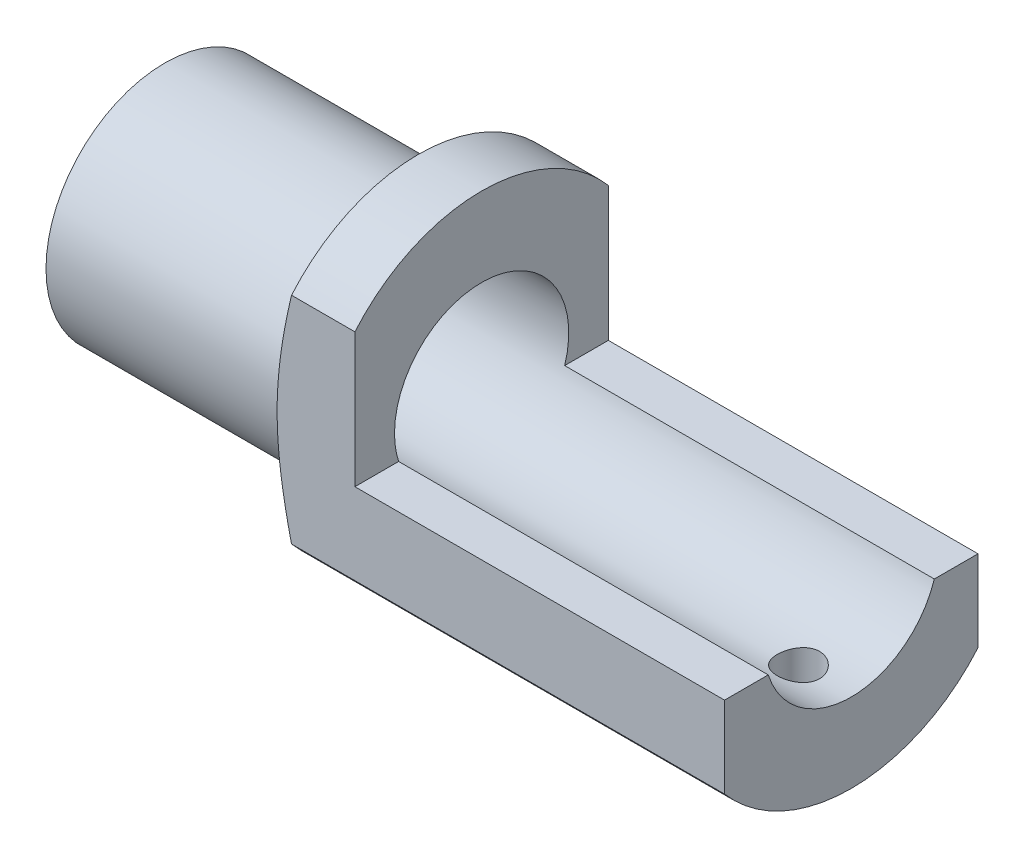
SolidWorks part; units mm, degrees
material "ПТФЭ (общий)"
ref_plane "Спереди" through (0, 0, 0) normal (0, 0, 1) x (1, 0, 0)
ref_plane "Сверху" through (0, 0, 0) normal (0, 1, 0) x (1, 0, 0)
ref_plane "Справа" through (0, 0, 0) normal (1, 0, 0) x (0, 0, -1)
sketch "Эскиз1" plane through (0, 0, 0) normal (0, 0, 1) x (1, 0, 0)
  line L0 (0, 0) -> (12.5645, 0) construction
  line L1 (0, 1.65) -> (13, 1.65)
  line L2 (13, 1.65) -> (13, 3.15)
  line L3 (13, 3.15) -> (4.5, 3.15)
  line L4 (4.5, 3.15) -> (4.5, 2.25)
  line L5 (4.5, 2.25) -> (0, 2.25)
  line L6 (0, 2.25) -> (0, 1.65)
  dimension "D1" = 3.3
  dimension "D2" = 4.5
  dimension "D3" = 6.3
  dimension "D4" = 13
  dimension "D5" = 4.5
revolve "Повернуть1" add sketch "Эскиз1" angle 360 about L0
sketch "Эскиз2" plane through (13, 0, 0) normal (1, 0, 0) x (0, 0, -1)
  line L0 (-3.1101, -0.5) -> (3.1101, -0.5)
  circle A0 centre (0, 0) radius 3.15 construction
  circle A1 centre (0, 0) radius 1.65 construction
  circle M1 centre (0, 0) radius 3.15
  dimension "D1" = 0.5
extrude "Вырез-Вытянуть1" cut sketch "Эскиз2" against normal offset from surface (7 mm away) 1.5 contours L0 M1
chamfer "Фаска1" distance 0.3 angle 70 1 edges at (4.5, 0, 3.15)
sketch "Эскиз3" plane through (0, -0.5, 0) normal (0, 1, 0) x (1, 0, 0)
  line L2 (6, 3.1101) -> (6, 1.5724) construction
  circle A0 centre (12, 0) radius 0.4
  dimension "D1" = 6
  dimension "D2" = 0.8
extrude "Вырез-Вытянуть2" cut sketch "Эскиз3" against normal blind 10
sketch "Эскиз4" plane through (6, 0, 0) normal (-1, 0, 0) x (0, 0, 1)
  line L0 (2.4, 2.0402) -> (2.4, -2.0402)
  line L1 (-2.4, 2.0402) -> (-3.6993, 2.0402)
  line L2 (-2.4, 2.0402) -> (-2.4, -2.0402)
  line L3 (-3.6993, 2.0402) -> (-3.6993, -2.0402)
  line L4 (-3.6993, -2.0402) -> (-2.4, -2.0402)
  line L5 (2.4, 2.0402) -> (4.028, 2.0402)
  line L6 (4.028, 2.0402) -> (4.028, -2.0402)
  line L7 (4.028, -2.0402) -> (2.4, -2.0402)
  arc A0 (3.1101, -0.5) -> (-3.1101, -0.5) centre (0, 0) ccw construction
  arc A1 (-3.1101, -0.5) -> (3.1101, -0.5) centre (0, 0) ccw construction
  arc A2 (1.5724, -0.5) -> (-1.5724, -0.5) centre (0, 0) ccw construction
  arc M9 (-3.1101, -0.5) -> (3.1101, -0.5) centre (0, 0) cw
  line M10 (3.1101, -0.5) -> (1.5724, -0.5)
  line M12 (-1.5724, -0.5) -> (-3.1101, -0.5)
  dimension "D1" = 2.4
extrude "Вырез-Вытянуть3" cut sketch "Эскиз4" along normal through all and the other way through all contours L4 L3 L1 L2 M9 M12 | L6 L7 L0 L5 M10 M9 | L2 M9 M12 | L0 M9 M10
